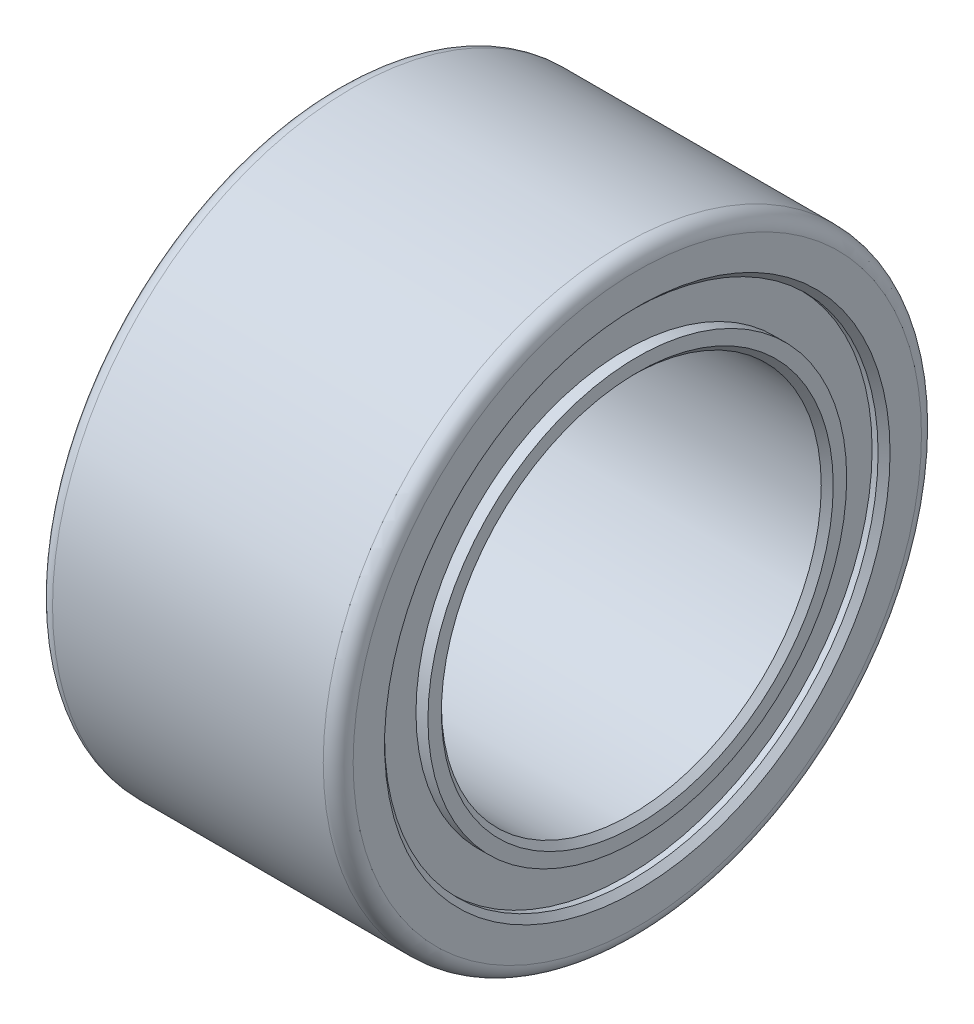
SolidWorks part; units mm, degrees
ref_plane "Front Plane" through (0, 0, 0) normal (0, 0, 1) x (1, 0, 0)
ref_plane "Top Plane" through (0, 0, 0) normal (0, 1, 0) x (1, 0, 0)
ref_plane "Right Plane" through (0, 0, 0) normal (1, 0, 0) x (0, 0, -1)
sketch "Sketch2" plane through (0, 0, 0) normal (1, 0, 0) x (0, 0, -1)
  circle A0 centre (0, 0) radius 5
  dimension "D1" = 10
extrude "Boss-Extrude1" add sketch "Sketch2" along normal mid plane 4.9784
sketch "Sketch3" plane through (2.4892, 0, 0) normal (1, 0, 0) x (0, 0, -1)
  circle A0 centre (0, 0) radius 3.175
  dimension "D1" = 6.35
extrude "Cut-Extrude1" cut sketch "Sketch3" against normal through all
sketch "Sketch4" plane through (2.4892, 0, 0) normal (1, 0, 0) x (0, 0, -1)
  circle A0 centre (0, 0) radius 3.5
  circle A1 centre (0, 0) radius 4.125
  dimension "D1" = 7
  dimension "D2" = 8.25
extrude "Cut-Extrude2" cut sketch "Sketch4" against normal blind 0.2
mirror "Mirror1" about plane through (0, 0, 0) normal (1, 0, 0) of "Cut-Extrude2"
chamfer "Chamfer1" distance 0.1 angle 45 4 edges at (-2.4892, 0, -3.175) (2.4892, 0, -4.125) (2.4892, 0, -3.175) (-2.4892, 0, -5)
fillet "Fillet1" radius 0.25 2 edges at (-2.3892, 0, -5) (2.4892, 0, -5)
